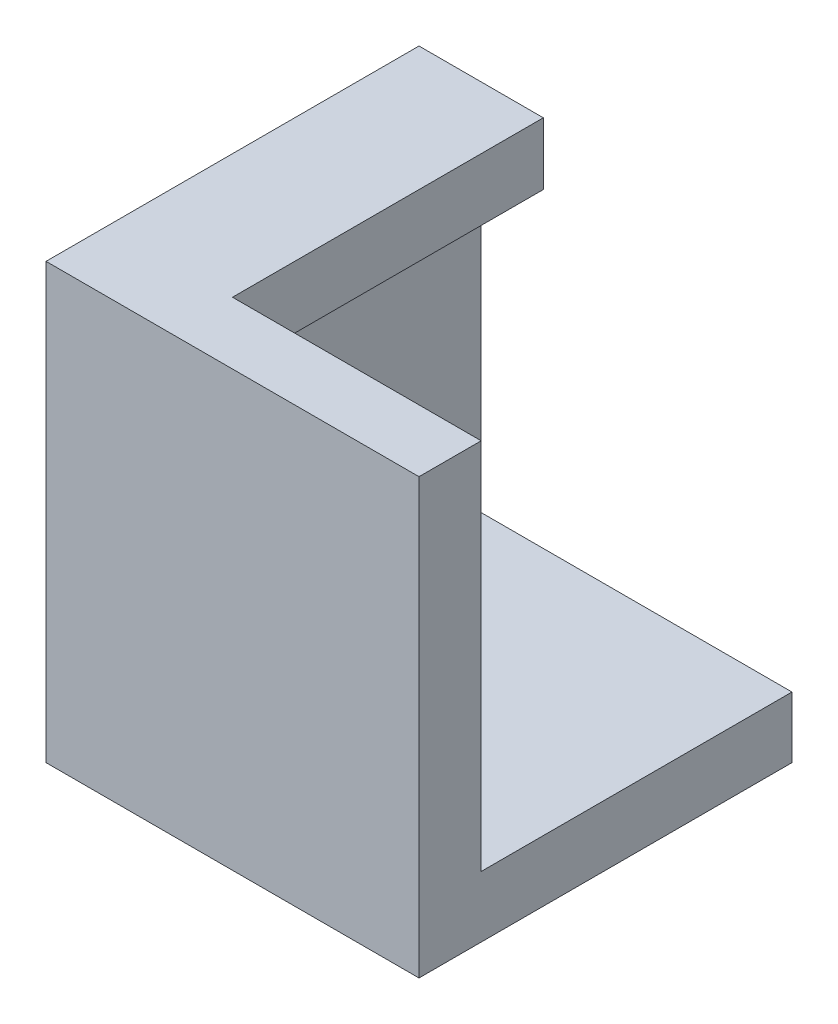
SolidWorks part; units mm, degrees
ref_plane "Front Plane" through (0, 0, 0) normal (0, 0, 1) x (1, 0, 0)
ref_plane "Top Plane" through (0, 0, 0) normal (0, 1, 0) x (1, 0, 0)
ref_plane "Right Plane" through (0, 0, 0) normal (1, 0, 0) x (0, 0, -1)
sketch "Sketch1" plane through (0, 0, 0) normal (0, 1, 0) x (1, 0, 0)
  line L1 (0, 0) -> (60.96, 0)
  line L2 (0, 0) -> (0, 60.96)
  line L3 (0, 60.96) -> (60.96, 60.96)
  line L4 (60.96, 0) -> (60.96, 60.96)
  dimension "D1" = 60.96
  dimension "D2" = 60.96
extrude "Boss-Extrude1" add sketch "Sketch1" along normal blind 10
sketch "Sketch2" plane through (0, 10, 0) normal (0, 1, 0) x (1, 0, 0)
  line L0 (0, 60.96) -> (10.16, 60.96)
  line L1 (60.96, 60.96) -> (0, 60.96) construction
  line L2 (10.16, 60.96) -> (10.16, 10.16)
  line L3 (10.16, 10.16) -> (60.96, 10.16)
  line L4 (60.96, 0) -> (60.96, 60.96) construction
  line L5 (60.96, 10.16) -> (60.96, 0)
  line L6 (60.96, 0) -> (0, 0)
  line L7 (0, 0) -> (0, 60.96)
  dimension "D1" = 10.16
  dimension "D2" = 10.16
extrude "Boss-Extrude2" add sketch "Sketch2" along normal blind 60.96 contours L2 L3 L5 L6 L7 L0
sketch "Sketch5" plane through (10.16, 0, 0) normal (1, 0, 0) x (0, 0, -1)
  line L0 (10.16, 70.96) -> (10.16, 10) construction
  line L1 (60.96, 70.96) -> (10.16, 70.96)
  line L2 (60.96, 70.96) -> (60.96, 60.8)
  line L3 (60.96, 60.8) -> (10.16, 60.8)
  line L4 (10.16, 70.96) -> (10.16, 60.8)
  dimension "D1" = 10.16
extrude "Boss-Extrude3" add sketch "Sketch5" along normal blind 10.16
sketch "Sketch6" plane through (0, 0, 0) normal (0, -1, 0) x (1, 0, 0)
  circle A0 centre (30.48, -30.48) radius 6.35
  dimension "D1" = 12.7
extrude "Cut-Extrude1" cut sketch "Sketch6" against normal blind 8.89
